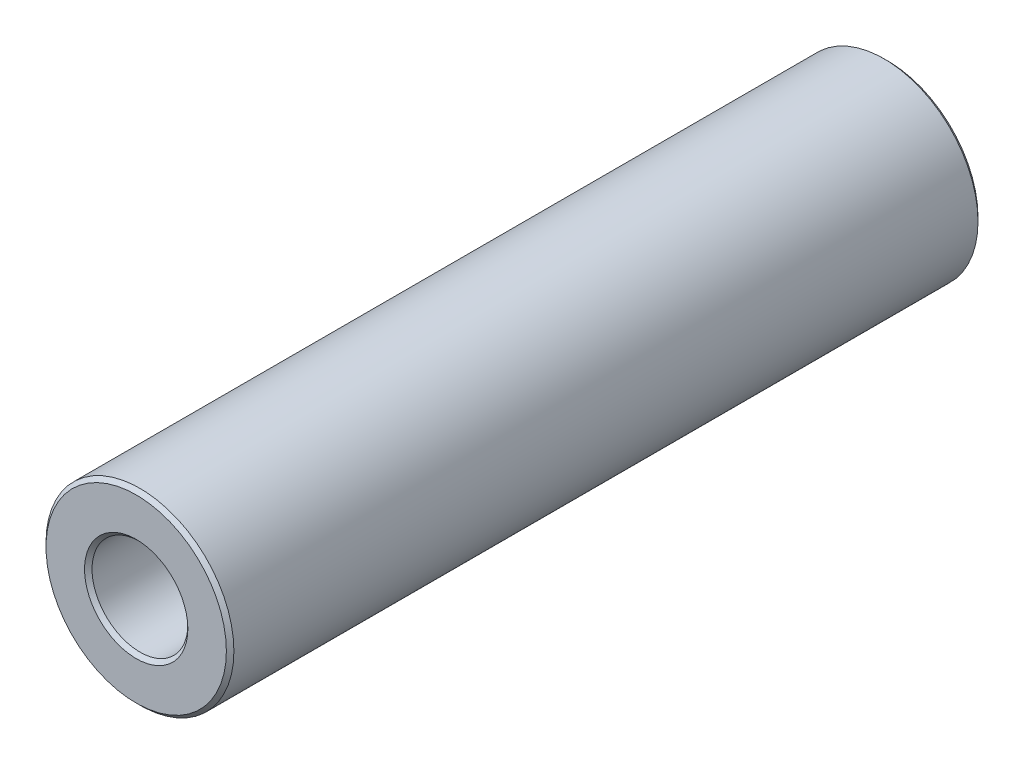
SolidWorks part; units mm, degrees
material "6061-T6 (SS)"
ref_plane "Front Plane" through (0, 0, 0) normal (0, 0, 1) x (1, 0, 0)
ref_plane "Top Plane" through (0, 0, 0) normal (0, 1, 0) x (1, 0, 0)
ref_plane "Right Plane" through (0, 0, 0) normal (1, 0, 0) x (0, 0, -1)
sketch "Sketch1" plane through (0, 0, 0) normal (0, 0, 1) x (1, 0, 0)
  circle A0 centre (0, 0) radius 2.55
  circle A1 centre (0, 0) radius 5
  dimension "D1" = 5.1
  dimension "D2" = 10
extrude "Boss-Extrude1" add sketch "Sketch1" along normal blind 40
chamfer "Chamfer1" distance 0.2 angle 45 4 edges at (5, 0, 0) (2.55, 0, 0) (2.55, 0, 40) (5, 0, 40)
